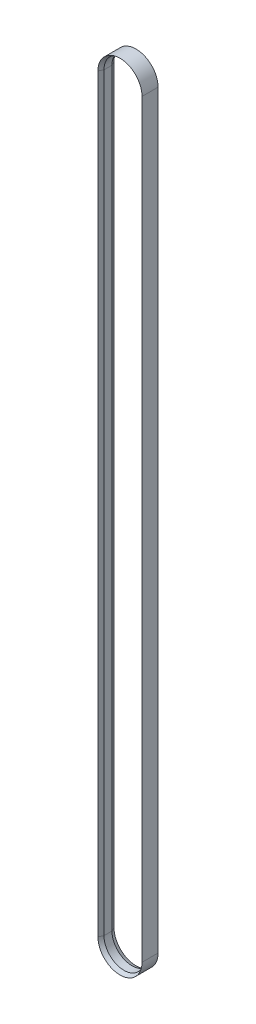
SolidWorks part; units mm, degrees
material "Silicon Rubber"
ref_plane "Front Plane" through (0, 0, 0) normal (0, 0, 1) x (1, 0, 0)
ref_plane "Top Plane" through (0, 0, 0) normal (0, 1, 0) x (1, 0, 0)
ref_plane "Right Plane" through (0, 0, 0) normal (1, 0, 0) x (0, 0, -1)
sketch "Sketch2" plane through (0, 0, 0) normal (0, 0, 1) x (1, 0, 0)
  line L0 (0, 0) -> (1, 0) construction
  line L1 (0, 0) -> (0, 1) construction
  line L2 (25, 0) -> (25, -935.5)
  line L3 (-25, -935.5) -> (-25, 0)
  arc A0 (-25, 0) -> (25, 0) centre (0, 0) cw
  arc A1 (25, -935.5) -> (-25, -935.5) centre (0, -935.5) cw
ref_plane "Plane1" through (0, 0, 0) normal (0, 1, 0) x (1, 0, 0)
sketch "Sketch3" plane through (0, 0, 0) normal (0, 1, 0) x (1, 0, 0)
  line L0 (25, 5) -> (25, -5)
  line L1 (-25, 0) -> (25, 0) construction
  line L2 (25, 5) -> (27.5, 10)
  line L3 (27.5, 10) -> (27.5, -10)
  line L4 (27.5, -10) -> (25, -5)
  dimension "D1" = 25
  dimension "D2" = 10
  dimension "D3" = 5
  dimension "D4" = 20
  dimension "D5" = 10
  dimension "D6" = 2.5
sweep "Sweep1" add profiles "Sketch3" path "Sketch2"
